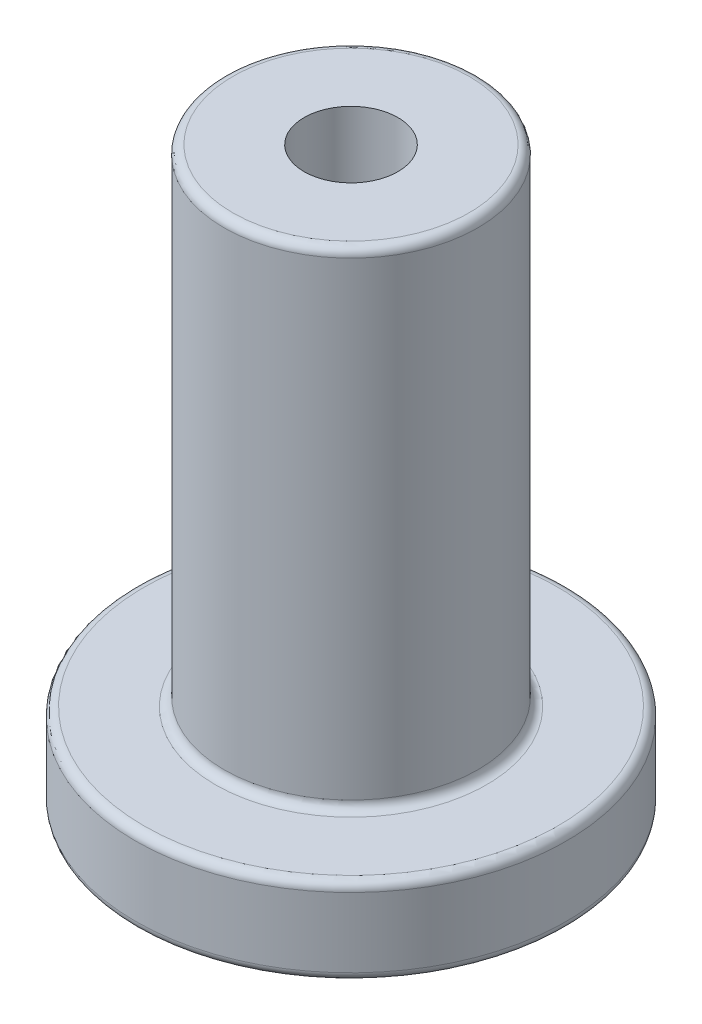
SolidWorks part; units mm, degrees
ref_plane "Front Plane" through (0, 0, 0) normal (0, 0, 1) x (1, 0, 0)
ref_plane "Top Plane" through (0, 0, 0) normal (0, 1, 0) x (1, 0, 0)
ref_plane "Right Plane" through (0, 0, 0) normal (1, 0, 0) x (0, 0, -1)
sketch "Sketch1" plane through (0, 0, 0) normal (0, 1, 0) x (1, 0, 0)
  circle A0 centre (0, 0) radius 12.4
  dimension "D1" = 24.8
extrude "Boss-Extrude1" add sketch "Sketch1" along normal blind 5
sketch "Sketch2" plane through (0, 5, 0) normal (0, 1, 0) x (1, 0, 0)
  circle A0 centre (0, 0) radius 7.3
  dimension "D1" = 14.6
extrude "Boss-Extrude2" add sketch "Sketch2" along normal blind 28
sketch "Sketch3" plane through (0, 33, 0) normal (0, 1, 0) x (1, 0, 0)
  circle A0 centre (0, 0) radius 2.7
  dimension "D1" = 5.4
extrude "Cut-Extrude1" cut sketch "Sketch3" against normal through all
sketch "Sketch4" plane through (0, 0, 0) normal (0, -1, 0) x (1, 0, 0)
  line L1 (-4.3802, 2.0818) -> (-3.993, -2.7525)
  line L2 (-3.993, -2.7525) -> (0.3872, -4.8343)
  line L3 (0.3872, -4.8343) -> (4.3802, -2.0818)
  line L4 (4.3802, -2.0818) -> (3.993, 2.7525)
  line L5 (3.993, 2.7525) -> (-0.3872, 4.8343)
  line L6 (-0.3872, 4.8343) -> (-4.3802, 2.0818)
  circle A0 centre (0, 0) radius 4.2 construction
  dimension "D1" = 8.4
extrude "Cut-Extrude2" cut sketch "Sketch4" against normal blind 3
fillet "Fillet1" radius 0.5 4 edges at (0, 0, 12.4) (0, 5, 12.4) (0, 33, 7.3) (0, 5, 7.3)
